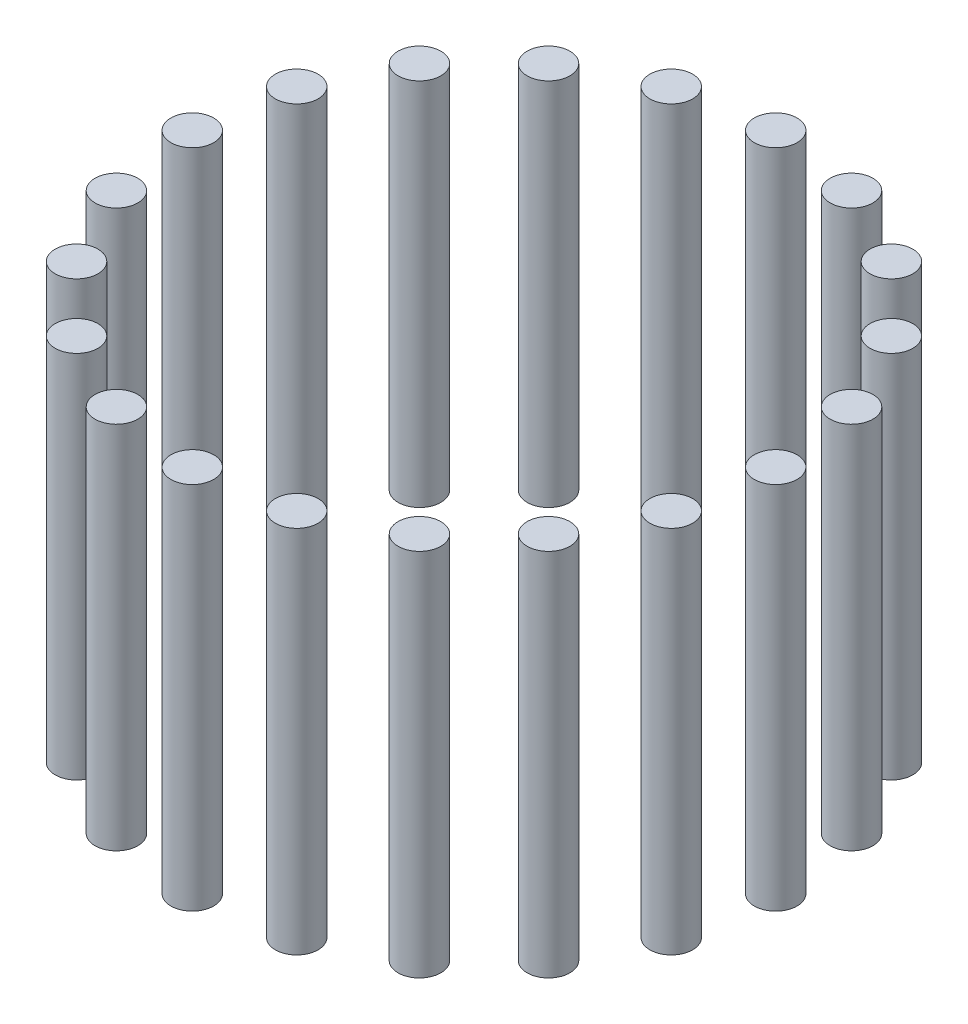
SolidWorks part; units mm, degrees
ref_plane "Front Plane" through (0, 0, 0) normal (0, 0, 1) x (1, 0, 0)
ref_plane "Top Plane" through (0, 0, 0) normal (0, 1, 0) x (1, 0, 0)
ref_plane "Right Plane" through (0, 0, 0) normal (1, 0, 0) x (0, 0, -1)
sketch "Sketch1" plane through (0, 0, 0) normal (0, 1, 0) x (1, 0, 0)
  circle A0 centre (0, 0) radius 75
  circle A1 centre (-75, 0) radius 5.5
  circle A2 centre (-71.3292, 23.1763) radius 5.5
  circle A3 centre (-60.6763, 44.0839) radius 5.5
  circle A4 centre (-44.0839, 60.6763) radius 5.5
  circle A5 centre (-23.1763, 71.3292) radius 5.5
  circle A6 centre (0, 75) radius 5.5
  circle A7 centre (23.1763, 71.3292) radius 5.5
  circle A8 centre (44.0839, 60.6763) radius 5.5
  circle A9 centre (60.6763, 44.0839) radius 5.5
  circle A10 centre (71.3292, 23.1763) radius 5.5
  circle A11 centre (75, 0) radius 5.5
  circle A12 centre (71.3292, -23.1763) radius 5.5
  circle A13 centre (60.6763, -44.0839) radius 5.5
  circle A14 centre (44.0839, -60.6763) radius 5.5
  circle A15 centre (23.1763, -71.3292) radius 5.5
  circle A16 centre (0, -75) radius 5.5
  circle A17 centre (-23.1763, -71.3292) radius 5.5
  circle A18 centre (-44.0839, -60.6763) radius 5.5
  circle A19 centre (-60.6763, -44.0839) radius 5.5
  circle A20 centre (-71.3292, -23.1763) radius 5.5
  point P45 (0, 0)
  dimension "D1" = 20
extrude "Boss-Extrude1" add sketch "Sketch1" along normal blind 95 contours A0 A17 | A0 A17 | A1 | A20 | A19 | A18 | A16 | A15 | A14 | A13 | A12 | A11 | A10 | A9 | A8 | A7 | A6 | A5 | A4 | A3 | A2
